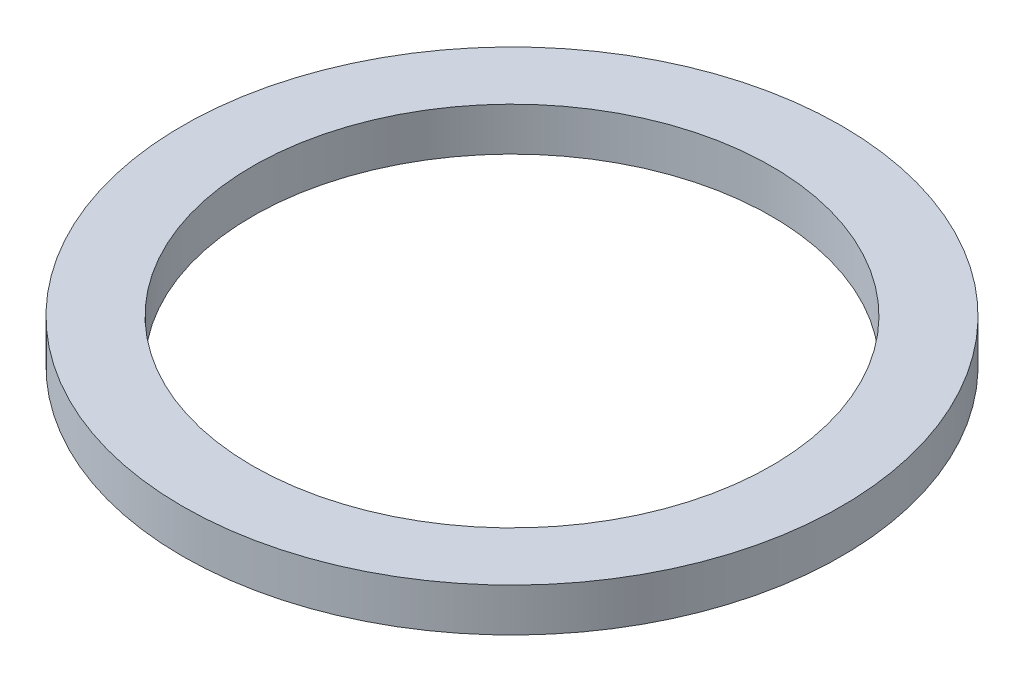
SolidWorks part; units mm, degrees
ref_plane "前视基准面" through (0, 0, 0) normal (0, 0, 1) x (1, 0, 0)
ref_plane "上视基准面" through (0, 0, 0) normal (0, 1, 0) x (1, 0, 0)
ref_plane "右视基准面" through (0, 0, 0) normal (1, 0, 0) x (0, 0, -1)
sketch "草图1" plane through (0, 0, 0) normal (0, 0, 1) x (1, 0, 0)
  line L0 (0, 77.1441) -> (0, -87.8701) construction
  line L1 (-61.6053, 0) -> (62.4304, 0) construction
  line L2 (15, 0) -> (15, 2.5)
  line L3 (19.05, 0) -> (19.05, 2.5)
  line L4 (15, 2.5) -> (19.05, 2.5)
  line L5 (15, 0) -> (19.05, 0)
  dimension "D1" = 15
  dimension "D2" = 19.05
  dimension "D3" = 2.5
revolve "旋转1" add sketch "草图1" angle 360 about L0
cosmetic thread "装饰螺纹线1" parameters "D2"=31
